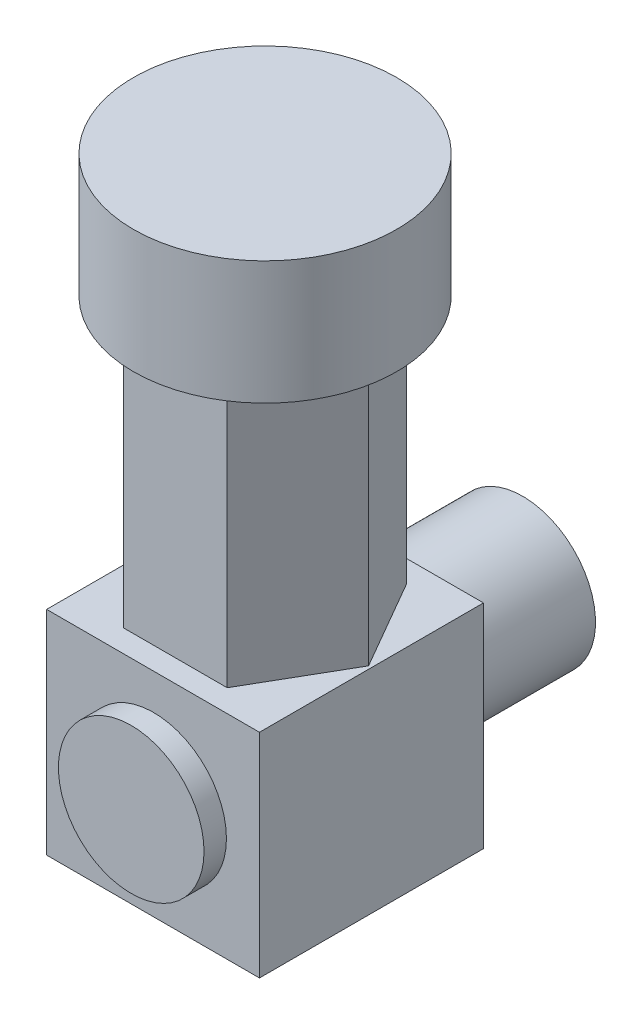
SolidWorks part; units mm, degrees
ref_plane "Front Plane" through (0, 0, 0) normal (0, 0, 1) x (1, 0, 0)
ref_plane "Top Plane" through (0, 0, 0) normal (0, 1, 0) x (1, 0, 0)
ref_plane "Right Plane" through (0, 0, 0) normal (1, 0, 0) x (0, 0, -1)
sketch "Sketch1" plane through (0, 0, 0) normal (0, 0, 1) x (1, 0, 0)
  line L1 (-4.3326, 9.2814) -> (14.6674, 9.2814)
  line L2 (-4.3326, 9.2814) -> (-4.3326, -9.7186)
  line L3 (-4.3326, -9.7186) -> (14.6674, -9.7186)
  line L4 (14.6674, 9.2814) -> (14.6674, -9.7186)
  dimension "D1" = 19
extrude "Boss-Extrude1" add sketch "Sketch1" along normal blind 20
sketch "Sketch2" plane through (0, 0, 20) normal (0, 0, 1) x (1, 0, 0)
  line L0 (-4.3326, -9.7186) -> (14.6674, 9.2814) construction
  circle A0 centre (5.219, -0.4121) radius 6.5
  dimension "D1" = 13
extrude "Boss-Extrude2" add sketch "Sketch2" along normal blind 2
sketch "Sketch3" plane through (0, 0, 0) normal (0, 0, -1) x (-1, 0, 0)
  line L0 (-14.6674, -9.7186) -> (4.3326, 9.2814) construction
  circle A0 centre (-5.1674, -0.2186) radius 6.5
  dimension "D1" = 13
extrude "Boss-Extrude3" add sketch "Sketch3" along normal blind 13
sketch "Sketch4" plane through (0, 9.2814, 0) normal (0, 1, 0) x (1, 0, 0)
  line L0 (-4.3326, -20) -> (14.6674, 0) construction
  line L2 (14.405, -10) -> (9.7862, -2)
  line L3 (9.7862, -2) -> (0.5486, -2)
  line L4 (0.5486, -2) -> (-4.0702, -10)
  line L5 (-4.0702, -10) -> (0.5486, -18)
  line L6 (0.5486, -18) -> (9.7862, -18)
  line L7 (9.7862, -18) -> (14.405, -10)
  circle A0 centre (5.1674, -10) radius 8 construction
  dimension "D1" = 16
extrude "Boss-Extrude4" add sketch "Sketch4" along normal blind 35
sketch "Sketch5" plane through (0, 44.2814, 0) normal (0, 1, 0) x (1, 0, 0)
  line L0 (0.5486, -18) -> (9.7862, -2) construction
  circle A0 centre (5.1674, -10) radius 11.75
  dimension "D1" = 23.5
extrude "Boss-Extrude5" add sketch "Sketch5" against normal blind 11
